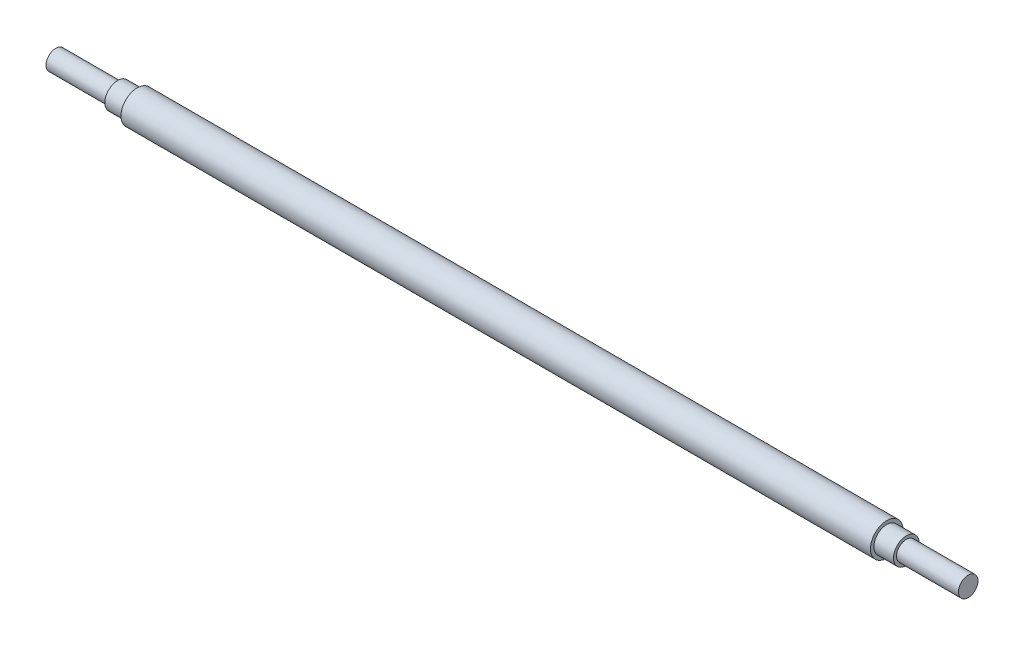
SolidWorks part; units mm, degrees
material "6061 合金"
ref_plane "前视基准面" through (0, 0, 0) normal (0, 0, 1) x (1, 0, 0)
ref_plane "上视基准面" through (0, 0, 0) normal (0, 1, 0) x (1, 0, 0)
ref_plane "右视基准面" through (0, 0, 0) normal (1, 0, 0) x (0, 0, -1)
sketch "草图1" plane through (0, 0, 0) normal (0, 0, 1) x (1, 0, 0)
  line L0 (-47.9121, 0) -> (64.1758, 0) construction
  line L1 (-27.3626, 0) -> (252.6374, 0)
  line L2 (252.6374, 0) -> (252.6374, 3)
  line L3 (252.6374, 3) -> (233.6374, 3)
  line L4 (233.6374, 3) -> (233.6374, 3.95)
  line L5 (233.6374, 3.95) -> (227.6374, 3.95)
  line L6 (227.6374, 3.95) -> (227.6374, 5)
  line L7 (227.6374, 5) -> (-2.3626, 5)
  line L8 (-2.3626, 5) -> (-2.3626, 3.95)
  line L9 (-2.3626, 3.95) -> (-8.3626, 3.95)
  line L10 (-8.3626, 3.95) -> (-8.3626, 3)
  line L11 (-8.3626, 3) -> (-27.3626, 3)
  line L12 (-27.3626, 3) -> (-27.3626, 0)
  dimension "D1" = 230
  dimension "D2" = 6
  dimension "D3" = 19
  dimension "D4" = 3
  dimension "D5" = 3.95
  dimension "D6" = 5
revolve "旋转1" add sketch "草图1" angle 360 about L0
